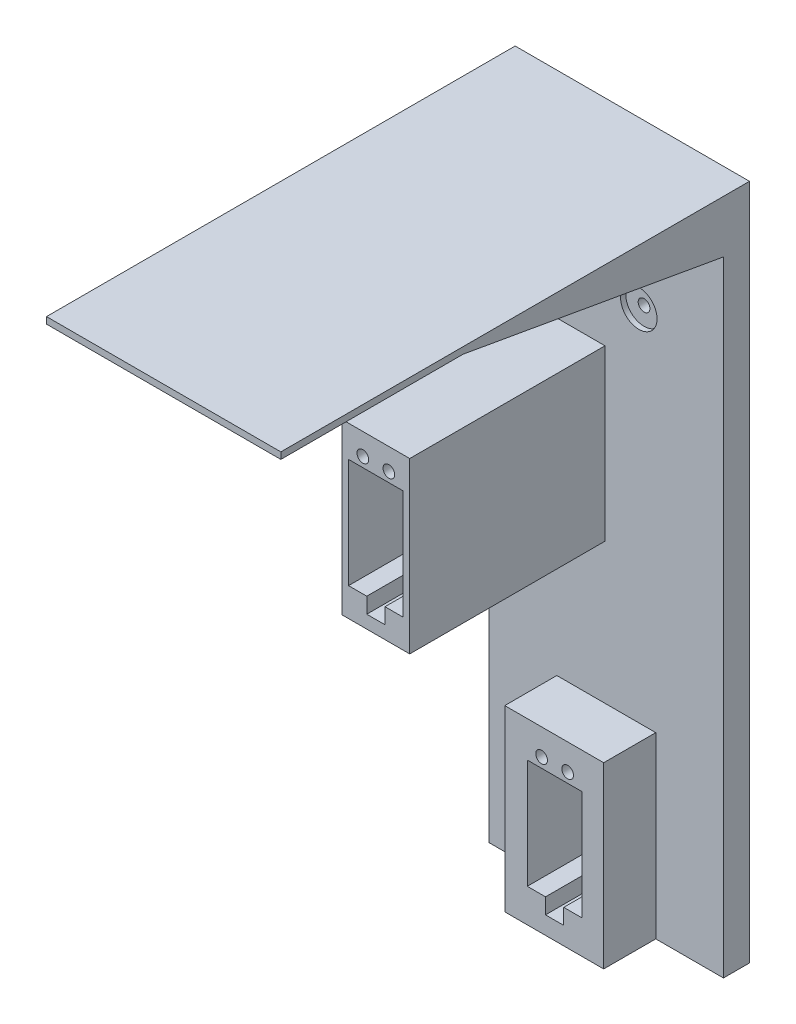
SolidWorks part; units mm, degrees
ref_plane "Front Plane" through (0, 0, 0) normal (0, 0, 1) x (1, 0, 0)
ref_plane "Top Plane" through (0, 0, 0) normal (0, 1, 0) x (1, 0, 0)
ref_plane "Right Plane" through (0, 0, 0) normal (1, 0, 0) x (0, 0, -1)
sketch "Sketch1" plane through (0, 0, 0) normal (0, 0, 1) x (1, 0, 0)
  line L1 (-75, 100) -> (75, 100)
  line L2 (-75, 100) -> (-75, -100)
  line L3 (-75, -100) -> (75, -100)
  line L4 (75, 100) -> (75, -100)
  line L5 (-75, 100) -> (75, -100) construction
  line L6 (-75, -100) -> (75, 100) construction
  point P0 (0, 0)
  dimension "D1" = 200
  dimension "D2" = 150
extrude "Boss-Extrude1" add sketch "Sketch1" along normal blind 30
sketch "Sketch2" plane through (0, 0, 30) normal (0, 0, 1) x (1, 0, 0)
  line L0 (75, -100) -> (75, 100) construction
  line L1 (-75, 100) -> (75, 100)
  line L2 (-75, 100) -> (-75, 90)
  line L3 (-75, 90) -> (75, 90)
  line L4 (75, 100) -> (75, 90)
  dimension "D1" = 10
extrude "Boss-Extrude2" add sketch "Sketch2" along normal blind 150
sketch "Sketch3" plane through (0, 0, 30) normal (0, 0, 1) x (1, 0, 0)
  line L0 (0, -100) -> (0, 0)
  line L1 (-75, -100) -> (75, -100) construction
  line L4 (0, 46.5) -> (0, 71.5)
  line L9 (-10.3251, 73.9819) -> (12.4051, 43.2014) construction
  line L10 (-12.4051, 43.2014) -> (10.3251, 73.9819) construction
  line L11 (-39.5, 13) -> (-39.5, 7)
  line L25 (-43, 13) -> (-36, 7) construction
  line L26 (-43, 7) -> (-36, 13) construction
  line L27 (-15.8, 46.5) -> (-12.5, 46.5)
  line L28 (-12.5, 46.5) -> (12.5, 46.5)
  line L29 (-12.5, 59) -> (12.5, 59)
  line L30 (12.5, 46.5) -> (-12.5, 46.5)
  line L31 (12.5, 46.5) -> (12.5, 71.5)
  line L32 (12.5, 71.5) -> (-12.5, 71.5)
  line L33 (-12.5, 46.5) -> (-12.5, 71.5)
  circle A0 centre (12.5, 46.5) radius 1.65
  circle A1 centre (-12.5, 46.5) radius 2.25
  circle A2 centre (12.5, 71.5) radius 1.65
  circle A3 centre (-12.5, 71.5) radius 2.25
  circle A4 centre (-12.5, 71.5) radius 3.3
  circle A5 centre (12.5, 71.5) radius 3.3
  circle A6 centre (12.5, 46.5) radius 3.3
  circle A7 centre (-12.5, 46.5) radius 3.3
  point P5 (0, 60)
  point P22 (-39.5, 10)
  dimension "D13" = 3.3
  dimension "D14" = 6.6
  dimension "D2" = 4.5
  dimension "D3" = 3.3
  dimension "D4" = 3.3
  dimension "D7" = 6
  dimension "D8" = 7
  dimension "D11" = 25
  dimension "D12" = 25
extrude "Cut-Extrude3" cut sketch "Sketch3" against normal blind 80
ref_plane "Plane1" through (0, 0, 30) normal (0, 0, 1) x (1, 0, 0)
sketch "Sketch6" plane through (0, 0, 30) normal (0, 0, 1) x (1, 0, 0)
  circle A0 centre (-12.5, 71.5) radius 5
  circle A1 centre (12.5, 71.5) radius 5
  circle A2 centre (-12.5, 46.5) radius 5
  circle A3 centre (12.5, 46.5) radius 5
  dimension "D1" = 10
  dimension "D2" = 10
  dimension "D3" = 10
  dimension "D4" = 10
extrude "Cut-Extrude5" cut sketch "Sketch6" against normal blind 22
sketch "Sketch7" plane through (0, 0, 8) normal (0, 0, 1) x (1, 0, 0)
  circle A0 centre (-12.5, 71.5) radius 1.925
  circle A1 centre (12.5, 71.5) radius 1.925
  circle A2 centre (-12.5, 46.5) radius 1.925
  circle A3 centre (12.5, 46.5) radius 1.925
  dimension "D1" = 3.85
  dimension "D2" = 3.85
  dimension "D3" = 3.85
  dimension "D4" = 3.85
extrude "Cut-Extrude6" cut sketch "Sketch7" against normal blind 5
sketch "Sketch9" plane through (0, 0, 30) normal (0, 0, 1) x (1, 0, 0)
  line L0 (-12.5, 46.5) -> (12.5, 46.5)
  line L1 (12.5, 46.5) -> (0, 46.5)
  line L2 (0, 46.5) -> (1.1812, -69.9316)
  line L3 (1.1812, -69.9316) -> (1.1812, -115.5276)
  line L4 (-13.5, 15.5) -> (0.3145, 15.5)
  line L5 (-2.604, -89.8179) -> (4.396, -89.8179)
  line L6 (11.396, -83.8179) -> (11.396, -41.8179)
  line L7 (-2.604, -83.8179) -> (-9.604, -83.8179)
  line L8 (4.396, -89.8179) -> (4.396, -83.8179)
  line L9 (4.396, -83.8179) -> (11.396, -83.8179)
  line L10 (-9.604, -41.8179) -> (-9.604, -83.8179)
  line L11 (-24, 15.5) -> (-3, 15.5)
  line L12 (-17, -26.5) -> (-24, -26.5)
  line L18 (-24, 15.5) -> (-24, -26.5)
  line L19 (-10, -32.5) -> (-10, -26.5)
  line L20 (-17, -32.5) -> (-10, -32.5)
  line L21 (-17, -26.5) -> (-17, -32.5)
  line L22 (-10, -26.5) -> (-3, -26.5)
  line L23 (-3, -26.5) -> (-3, 15.5)
  line L24 (-9.604, -41.8179) -> (11.396, -41.8179)
  line L25 (-2.604, -83.8179) -> (-2.604, -89.8179)
  circle A6 centre (-8.5, 19.25) radius 2.08
  circle A7 centre (-18.5, 19.25) radius 2.08
  circle A8 centre (5.896, -38.0679) radius 2.08
  circle A9 centre (-4.104, -38.0679) radius 2.08
  point P16 (-39.5, 65.9329)
  dimension "D6" = 42
  dimension "D1" = 13.8145
fillet "Fillet1" radius 5 1 edges at (0, 90, 30)
extrude "Cut-Extrude7" cut sketch "Sketch9" against normal blind 30 contours L22 L23 L11 L18 L12 L21 L20 L19 | A7 | A6
sketch "Sketch10" plane through (0, 0, 30) normal (0, 0, 1) x (1, 0, 0)
  line L8 (0.1568, -107.5662) -> (0.1568, -105.9215)
  line L9 (8.2068, -105.9215) -> (-7.8932, -105.9215) construction
ref_plane "Plane2" through (0, 0, 0) normal (0, 0, -1) x (-1, 0, 0)
sketch "Sketch12" plane through (0, 0, 0) normal (0, 0, -1) x (-1, 0, 0)
  line L0 (13.5, 15.5) -> (13.5, -37.4614)
  line L1 (24, 15.5) -> (3, 15.5) construction
  line L2 (13.5, -37.4614) -> (26.5, -37.4614)
  line L3 (26.5, -37.4614) -> (26.5, 27.5386)
  line L4 (3, 15.5) -> (3, -26.5)
  line L5 (26.5, -37.4614) -> (0.5, -37.4614)
  line L6 (26.5, -37.4614) -> (26.5, 27.5386)
  line L7 (26.5, 27.5386) -> (0.5, 27.5386)
  line L8 (0.5, -37.4614) -> (0.5, 27.5386)
  line L9 (3, -26.5) -> (10, -26.5)
  line L10 (10, -26.5) -> (10, -32.5)
  line L11 (10, -32.5) -> (17, -32.5)
  line L12 (17, -32.5) -> (17, -26.5)
  line L13 (17, -26.5) -> (24, -26.5)
  line L14 (24, -26.5) -> (24, 15.5)
  line L15 (24, 15.5) -> (3, 15.5)
  circle A0 centre (8.5, 19.25) radius 2.08
  circle A1 centre (18.5, 19.25) radius 2.08
  dimension "D1" = 13
  dimension "D2" = 65
  dimension "D3" = 26
  dimension "D4" = 65
extrude "Boss-Extrude5" add sketch "Sketch12" against normal blind 85
sketch "Sketch13" plane through (0, 0, 0) normal (0, 0, -1) x (-1, 0, 0)
  line L0 (-75, -100) -> (-75, -160)
  line L1 (-75, -160) -> (75, -160)
  line L2 (75, -160) -> (75, -100)
  line L3 (75, -100) -> (-75, -100) construction
  line L4 (75, -100) -> (-75, -100)
  dimension "D1" = 60
extrude "Boss-Extrude6" add sketch "Sketch13" against normal blind 30
sketch "Sketch15" plane through (0, 0, 30) normal (0, 0, 1) x (1, 0, 0)
  line L0 (-10.3432, -105.1715) -> (10.6568, -105.1715)
  line L1 (10.6568, -105.1715) -> (10.6568, -147.1715)
  line L2 (10.6568, -147.1715) -> (3.6568, -147.1715)
  line L3 (3.6568, -147.1715) -> (3.6568, -153.1715)
  line L4 (3.6568, -153.1715) -> (-3.3432, -153.1715)
  line L5 (-3.3432, -153.1715) -> (-3.3432, -147.1715)
  line L6 (-3.3432, -147.1715) -> (-10.3432, -147.1715)
  line L7 (-10.3432, -147.1715) -> (-10.3432, -105.1715)
  circle A0 centre (-4.8432, -101.4215) radius 2.08
  circle A1 centre (5.1568, -101.4215) radius 2.08
  dimension "D1" = 4.16
  dimension "D2" = 4.16
extrude "Cut-Extrude8" cut sketch "Sketch15" against normal blind 30
sketch "Sketch16" plane through (0, 0, 30) normal (0, 0, 1) x (1, 0, 0)
  circle A0 centre (-12.5, 71.5) radius 7
  circle A1 centre (12.5, 71.5) radius 7
  circle A2 centre (12.5, 46.5) radius 7
  circle A3 centre (-12.5, 46.5) radius 7
  dimension "D1" = 14
extrude "Cut-Extrude9" cut sketch "Sketch16" against normal blind 22
sketch "Sketch17" plane through (0, 0, 0) normal (0, 0, -1) x (-1, 0, 0)
  line L0 (-75, -160) -> (75, -160) construction
  line L1 (75, 100) -> (55, 100)
  line L2 (75, 100) -> (75, -160)
  line L3 (75, -160) -> (55, -160)
  line L4 (55, 100) -> (55, -160)
  line L5 (-55, -160) -> (-75, -160)
  line L6 (-75, 100) -> (-75, -160)
  line L7 (-55, 100) -> (-75, 100)
  line L8 (-55, 100) -> (-55, -160)
  dimension "D1" = 20
extrude "Cut-Extrude10" cut sketch "Sketch17" against normal blind 180
sketch "Sketch19" plane through (0, 0, 30) normal (0, 0, 1) x (1, 0, 0)
  line L0 (-55, 85) -> (55, 85)
  line L1 (55, 85) -> (55, -160)
  line L2 (55, -160) -> (19, -160)
  line L3 (55, -160) -> (-55, -160) construction
  line L4 (19, -160) -> (19, -91.3882)
  line L5 (19, -91.3882) -> (-19, -91.3882)
  line L6 (-19, -91.3882) -> (-19, -160)
  line L7 (-19, -160) -> (-55, -160)
  line L8 (-55, -160) -> (-55, 85)
  line L9 (-26.5, 27.5386) -> (-26.5, -37.4614)
  line L10 (-26.5, -37.4614) -> (-0.5, -37.4614) construction
  line L11 (-26.5, 27.5386) -> (-26.5, -37.4614) construction
  line L12 (-26.5, -37.4614) -> (-0.5, -37.4614)
  line L13 (-0.5, -37.4614) -> (-0.5, 27.5386)
  line L14 (-0.5, 27.5386) -> (-26.5, 27.5386)
  dimension "D1" = 36
  dimension "D2" = 36
extrude "Cut-Extrude11" cut sketch "Sketch19" against normal blind 20
sketch "Sketch20" plane through (0, 0, 10) normal (0, 0, 1) x (1, 0, 0)
  line L1 (-55, 85) -> (55, 85)
  line L2 (-55, 85) -> (-55, 97.4806)
  line L3 (-55, 97.4806) -> (55, 97.4806)
  line L4 (55, 85) -> (55, 97.4806)
extrude "Cut-Extrude12" cut sketch "Sketch20" along normal blind 200
sketch "Sketch21" plane through (0, 0, 0) normal (0, 0, -1) x (-1, 0, 0)
  line L0 (-55, -160) -> (55, -160) construction
  line L1 (55, 100) -> (45, 100)
  line L2 (55, 100) -> (55, -160)
  line L3 (55, -160) -> (45, -160)
  line L4 (45, 100) -> (45, -160)
  line L5 (-45, -160) -> (-55, -160)
  line L6 (-45, 100) -> (-55, 100)
  line L7 (-45, 100) -> (-45, -160)
  line L8 (-55, 100) -> (-55, -160)
  dimension "D1" = 10
extrude "Cut-Extrude13" cut sketch "Sketch21" against normal blind 200
sketch "Sketch22" plane through (0, 0, 0) normal (0, 0, -1) x (-1, 0, 0)
  line L1 (3, 15.5) -> (24.0007, 15.5)
  line L2 (3, 15.5) -> (3, 25.5)
  line L3 (3, 25.5) -> (24.0007, 25.5)
  line L4 (24.0007, 15.5) -> (24.0007, 25.5)
  dimension "D1" = 10
extrude "Cut-Extrude14" cut sketch "Sketch22" against normal blind 80
sketch "Sketch24" plane through (0, 0, 0) normal (0, 0, -1) x (-1, 0, 0)
  line L1 (10.3432, -105.1715) -> (-10.534, -105.1715)
  line L2 (10.3432, -105.1715) -> (10.3432, -95.6715)
  line L3 (10.3432, -95.6715) -> (-10.534, -95.6715)
  line L4 (-10.534, -105.1715) -> (-10.534, -95.6715)
  dimension "D1" = 9.5
extrude "Cut-Extrude15" cut sketch "Sketch24" against normal blind 25
sketch "Sketch25" plane through (0, 0, 8) normal (0, 0, 1) x (1, 0, 0)
  circle A0 centre (12.5, 71.5) radius 2.25
  dimension "D1" = 4.5
extrude "Cut-Extrude16" cut sketch "Sketch25" against normal blind 10
sketch "Sketch26" plane through (0, 0, 8) normal (0, 0, 1) x (1, 0, 0)
  circle A0 centre (12.5, 46.5) radius 2.25
  dimension "D1" = 4.5
extrude "Cut-Extrude17" cut sketch "Sketch26" against normal blind 10
sketch "Sketch27" plane through (0, 0, 85) normal (0, 0, 1) x (1, 0, 0)
  circle A0 centre (-18.5, 19.25) radius 2.25
  dimension "D1" = 4.5
extrude "Cut-Extrude18" cut sketch "Sketch27" against normal blind 10
sketch "Sketch28" plane through (0, 0, 85) normal (0, 0, 1) x (1, 0, 0)
  circle A0 centre (-8.5, 19.25) radius 2.25
  dimension "D1" = 4.5
extrude "Cut-Extrude19" cut sketch "Sketch28" against normal blind 10
sketch "Sketch29" plane through (0, 0, 30) normal (0, 0, 1) x (1, 0, 0)
  circle A0 centre (-4.8432, -101.4215) radius 2.25
  circle A1 centre (5.1568, -101.4215) radius 2.25
  dimension "D1" = 4.5
  dimension "D2" = 4.5
extrude "Cut-Extrude20" cut sketch "Sketch29" against normal blind 10
ref_plane "Plane3" through (-45, 97.4806, 10) normal (0, -1, 0) x (-1, 0, 0)
chamfer "Chamfer2" distance 100 angle 10 1 edges at (0, 97.4806, 10)
sketch "Sketch33" plane through (0, 0, 10) normal (0, 0, 1) x (1, 0, 0)
  line L0 (45, 79.8479) -> (-45, 79.8479) construction
  line L1 (-40, 79.8479) -> (40, 79.8479)
  line L2 (0, 79.8479) -> (0, 97.4779)
  line L3 (-40, 97.4779) -> (40, 97.4779)
  line L4 (40, 79.8479) -> (40, 97.4779)
  line L5 (-40, 79.8479) -> (-40, 97.4779)
  line M8 (45, 79.8479) -> (-45, 79.8479)
  dimension "D1" = 17.63
  dimension "D2" = 40
sketch "Sketch35" plane through (45, 0, 0) normal (1, 0, 0) x (0, 0, -1)
  line L0 (-110, 97.4806) -> (0, 97.4806)
  line L1 (0, -160) -> (0, 100) construction
  line L2 (-10, 79.8479) -> (-10, 97.4806)
extrude "Cut-Extrude21" cut sketch "Sketch33" along normal blind 170 contours L5 L1 L2 L3 | L4 L3 L2 M8
